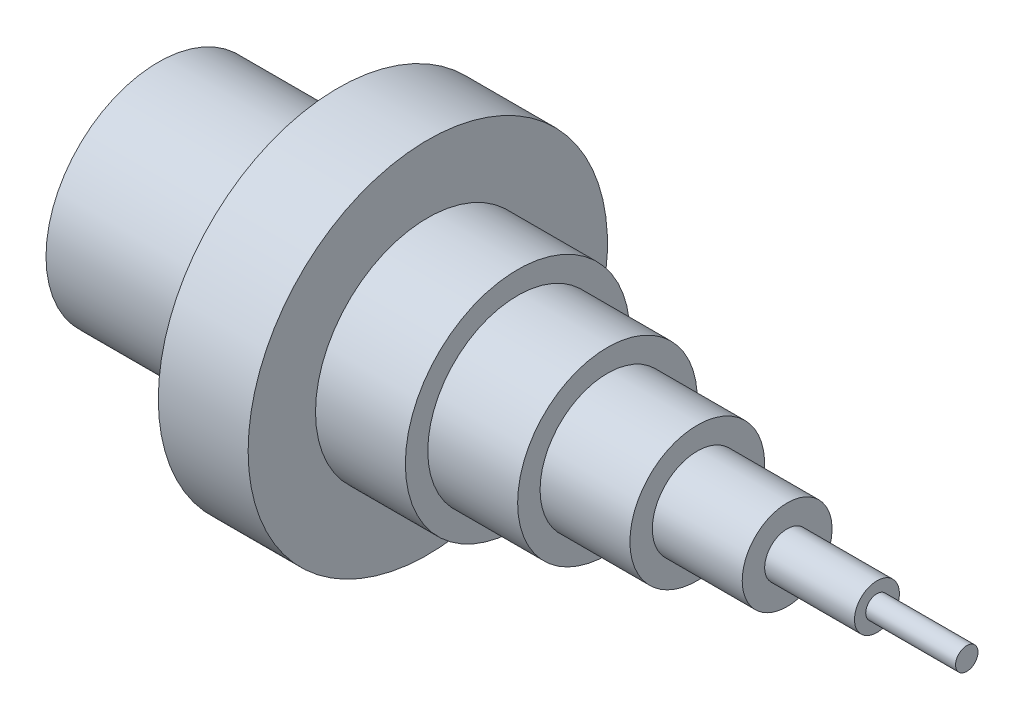
SolidWorks part; units mm, degrees
ref_plane "Front Plane" through (0, 0, 0) normal (0, 0, 1) x (1, 0, 0)
ref_plane "Top Plane" through (0, 0, 0) normal (0, 1, 0) x (1, 0, 0)
ref_plane "Right Plane" through (0, 0, 0) normal (1, 0, 0) x (0, 0, -1)
sketch "Sketch1" plane through (0, 0, 0) normal (0, 0, 1) x (1, 0, 0)
  line L0 (0, 0) -> (4572, 0) construction
  line L1 (4064, -127) -> (3556, -127)
  line L2 (4064, -63.5) -> (4064, -127)
  line L3 (3556, -127) -> (3556, -254)
  line L4 (1016, -635) -> (1016, -1016)
  line L5 (1016, -1016) -> (1524, -1016)
  line L6 (1524, -1016) -> (1524, -635)
  line L7 (2032, -508) -> (2032, -635)
  line L8 (2032, -635) -> (1524, -635)
  line L9 (3556, -254) -> (3048, -254)
  line L10 (2540, -381) -> (2540, -508)
  line L11 (2540, -508) -> (2032, -508)
  line L12 (4572, 0) -> (4572, -63.5)
  line L13 (3048, -254) -> (3048, -381)
  line L14 (3048, -381) -> (2540, -381)
  line L15 (4572, -63.5) -> (4064, -63.5)
  line L16 (1016, -635) -> (0, -635)
  line L17 (0, -635) -> (0, 0)
  line L18 (0, 0) -> (4572, 0)
  line L19 (-1339.2063, 0) -> (5077.3884, 0) construction
  dimension "D1" = 1270
  dimension "D2" = 2032
  dimension "D3" = 1016
  dimension "D4" = 4572
  dimension "D5" = 762
  dimension "D6" = 508
  dimension "D7" = 254
  dimension "D8" = 127
  dimension "D11" = 1016
  dimension "D16" = 508
revolve "Revolve1" add sketch "Sketch1" angle 360 about L0
sketch "Sketch3" plane through (0, 0, 0) normal (-1, 0, 0) x (0, 0, 1)
  circle A0 centre (0, 0) radius 508
extrude "Cut-Extrude2" cut sketch "Sketch3" against normal blind 1016
